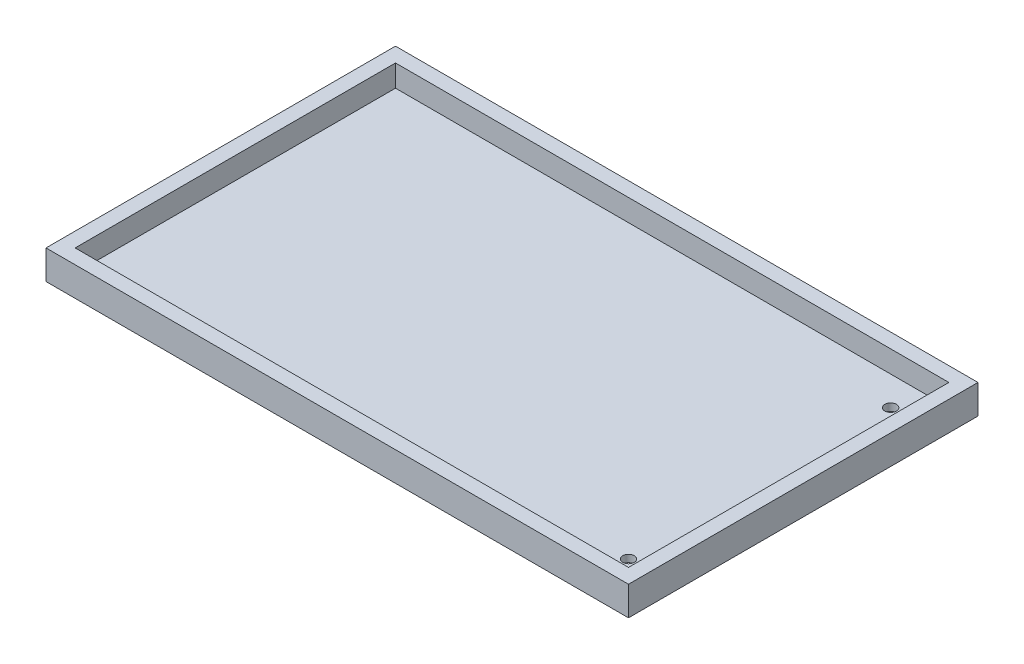
SolidWorks part; units mm, degrees
ref_plane "Front Plane" through (0, 0, 0) normal (0, 0, 1) x (1, 0, 0)
ref_plane "Top Plane" through (0, 0, 0) normal (0, 1, 0) x (1, 0, 0)
ref_plane "Right Plane" through (0, 0, 0) normal (1, 0, 0) x (0, 0, -1)
sketch "Sketch1" plane through (-10.8261, 0, 0) normal (0, 1, 0) x (1, 0, 0)
  line L1 (-56.8699, 25.0732) -> (44.7301, 25.0732)
  line L2 (-56.8699, 25.0732) -> (-56.8699, -35.8868)
  line L3 (-56.8699, -35.8868) -> (44.7301, -35.8868)
  line L4 (44.7301, 25.0732) -> (44.7301, -35.8868)
  dimension "D1" = 101.6
  dimension "D2" = 60.96
extrude "Boss-Extrude1" add sketch "Sketch1" along normal blind 5.08
sketch "Sketch2" plane through (-10.8261, 5.08, -21.0221) normal (0, 1, 0) x (1, 0, 0)
  line L1 (-54.3299, 1.511) -> (42.1901, 1.511)
  line L2 (-54.3299, 1.511) -> (-54.3299, -54.369)
  line L3 (-54.3299, -54.369) -> (42.1901, -54.369)
  line L4 (42.1901, 1.511) -> (42.1901, -54.369)
  line L8 (44.7301, 4.051) -> (-56.8699, 4.051) construction
  line L9 (44.7301, -56.909) -> (44.7301, 4.051) construction
  line L10 (-56.8699, -56.909) -> (44.7301, -56.909) construction
  line L11 (-56.8699, 4.051) -> (-56.8699, -56.909) construction
  dimension "D1" = 2.54
  dimension "D2" = 2.54
  dimension "D3" = 2.54
  dimension "D4" = 2.54
extrude "Cut-Extrude1" cut sketch "Sketch2" against normal blind 3.81
sketch "Sketch3" plane through (0, 1.27, -21.0221) normal (0, 1, 0) x (1, 0, 0)
  line L3 (33.904, -56.909) -> (33.904, 4.051) construction
  line L5 (31.364, 1.511) -> (-65.156, 1.511) construction
  circle A0 centre (26.284, -3.569) radius 1.016
  circle A1 centre (26.284, -49.289) radius 1.016
  point P8 (0, 0)
  dimension "D1" = 45.72
  dimension "D3" = 7.62
  dimension "D2" = 5.08
extrude "Cut-Extrude3" cut sketch "Sketch3" against normal blind 11.43
